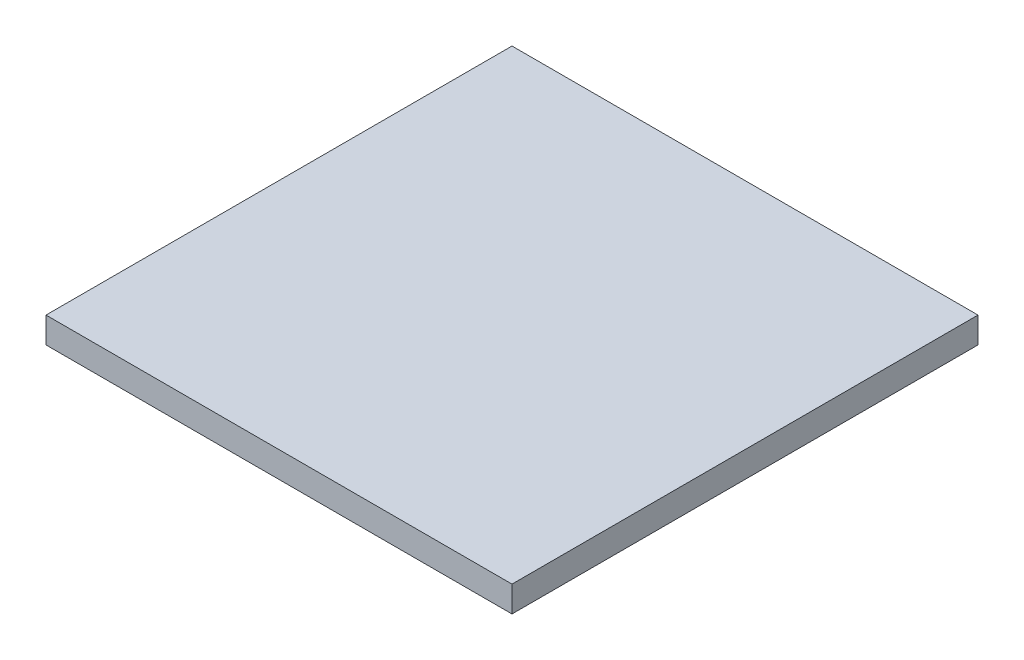
SolidWorks part; units mm, degrees
material "Glas"
ref_plane "Vorne" through (0, 0, 0) normal (0, 0, 1) x (1, 0, 0)
ref_plane "Oben" through (0, 0, 0) normal (0, 1, 0) x (1, 0, 0)
ref_plane "Rechts" through (0, 0, 0) normal (1, 0, 0) x (0, 0, -1)
sketch "Skizze1" plane through (0, 0, 0) normal (0, 1, 0) x (1, 0, 0)
  line L0 (-3.15, 3.15) -> (3.15, -3.15) construction
  line L1 (-3.15, 3.15) -> (3.15, 3.15)
  line L2 (-3.15, 3.15) -> (-3.15, -3.15)
  line L3 (-3.15, -3.15) -> (3.15, -3.15)
  line L4 (3.15, 3.15) -> (3.15, -3.15)
  dimension "D1" = 6.3
extrude "Aufsatz-Linear austragen1" add sketch "Skizze1" along normal blind 0.35
